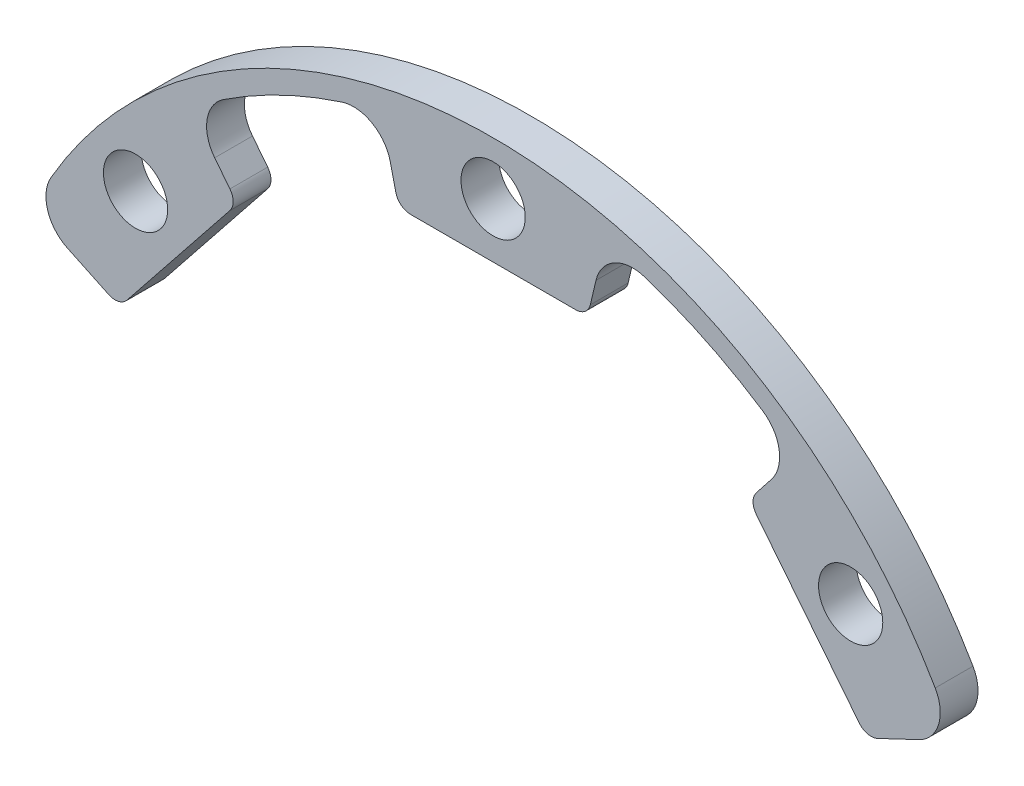
SolidWorks part; units mm, degrees
ref_plane "Plan de face" through (0, 0, 0) normal (0, 0, 1) x (1, 0, 0)
ref_plane "Plan de dessus" through (0, 0, 0) normal (0, 1, 0) x (1, 0, 0)
ref_plane "Plan de droite" through (0, 0, 0) normal (1, 0, 0) x (0, 0, -1)
sketch "Esquisse1" plane through (0, 0, 0) normal (0, 0, 1) x (1, 0, 0)
  circle A0 centre (0, 0) radius 67.5
  circle A1 centre (0, 60.5) radius 4.25
  circle A2 centre (47.3008, 37.7211) radius 4.25
  circle A3 centre (58.9831, -13.4625) radius 4.25
  circle A4 centre (26.25, -54.5086) radius 4.25
  circle A5 centre (-26.25, -54.5086) radius 4.25
  circle A6 centre (-58.9831, -13.4625) radius 4.25
  circle A7 centre (-47.3008, 37.7211) radius 4.25
  circle A8 centre (0, 0) radius 15
  point P19 (0, 0)
  dimension "D1" = 135
  dimension "D2" = 8.5
  dimension "D5" = 30
  dimension "D3" = 60.5
  dimension "D4" = 7
sketch "Esquisse2" plane through (0, 0, 0) normal (0, 0, 1) x (1, 0, 0)
  line L0 (0, 0) -> (-60.9953, 28.9105) construction
  line L1 (0, 0) -> (60.9953, 28.9105) construction
  line L2 (0, 0) -> (0, 67.5) construction
  line L3 (-32.9407, 41.8387) -> (-41.7558, 53.0349)
  line L4 (-12.1726, 51.84) -> (-15.4301, 65.7127)
  line L5 (12.1726, 51.84) -> (15.4301, 65.7127)
  line L6 (32.9407, 41.8387) -> (41.7558, 53.0349)
  line L7 (-48.1185, 22.8072) -> (-60.9953, 28.9105)
  line L8 (48.1185, 22.8072) -> (60.9953, 28.9105)
  line L9 (0, 0) -> (-47.3008, 37.7211) construction
  line L10 (0, 0) -> (-32.9407, 41.8387)
  line L11 (-49.4267, 23.4272) -> (-33.8366, 42.9766)
  line L12 (-12.5037, 53.25) -> (12.5037, 53.25)
  line L13 (33.8366, 42.9766) -> (49.4267, 23.4272)
  line L14 (0, 0) -> (47.3008, 37.7211) construction
  circle A0 centre (47.3008, 37.7211) radius 4.25 construction
  circle A1 centre (0, 60.5) radius 4.25 construction
  circle A2 centre (-47.3008, 37.7211) radius 4.25 construction
  circle A3 centre (47.3008, 37.7211) radius 4.25
  circle A4 centre (0, 60.5) radius 4.25
  circle A5 centre (-47.3008, 37.7211) radius 4.25
  circle A6 centre (0, 0) radius 67.5 construction
  arc A7 (-60.9953, 28.9105) -> (60.9953, 28.9105) centre (0, 0) cw
  arc A8 (-48.1185, 22.8072) -> (48.1185, 22.8072) centre (0, 0) cw
  arc A9 (-40.0546, 50.8742) -> (-14.8014, 63.0355) centre (0, 0) cw
  arc A10 (14.8014, 63.0355) -> (40.0546, 50.8742) centre (0, 0) cw
  arc A11 (-47.3008, 37.7211) -> (-37.4256, 47.535) centre (0, 0) cw construction
  arc A12 (0, 60.5) -> (-13.8299, 58.8981) centre (0, 0) ccw construction
  dimension "D3" = 53.25
  dimension "D6" = 64.75
  dimension "D1" = 64.64
  dimension "D2" = 64.64
  dimension "D4" = 25
  dimension "D5" = 25
  dimension "D7" = 13.211
  dimension "D8" = 13.214
extrude "Boss.-Extru.1" add sketch "Esquisse2" along normal blind 5 contours A7 L7 L11 L3 A5 | L3 A9 L4 A7 | A7 L4 L12 L5 A4 | L5 A10 L6 A7 | A7 L6 L13 L8 A3
fillet "Congé1" radius 5 6 edges at (-40.0546, 50.8742, 2.5) (-14.8014, 63.0355, 2.5) (14.8014, 63.0355, 2.5) (40.0546, 50.8742, 2.5) (60.9953, 28.9105, 2.5) (-60.9953, 28.9105, 2.5)
fillet "Congé2" radius 2 6 edges at (49.4267, 23.4272, 2.5) (33.8366, 42.9766, 2.5) (12.5037, 53.25, 2.5) (-12.5037, 53.25, 2.5) (-33.8366, 42.9766, 2.5) (-49.4267, 23.4272, 2.5)
